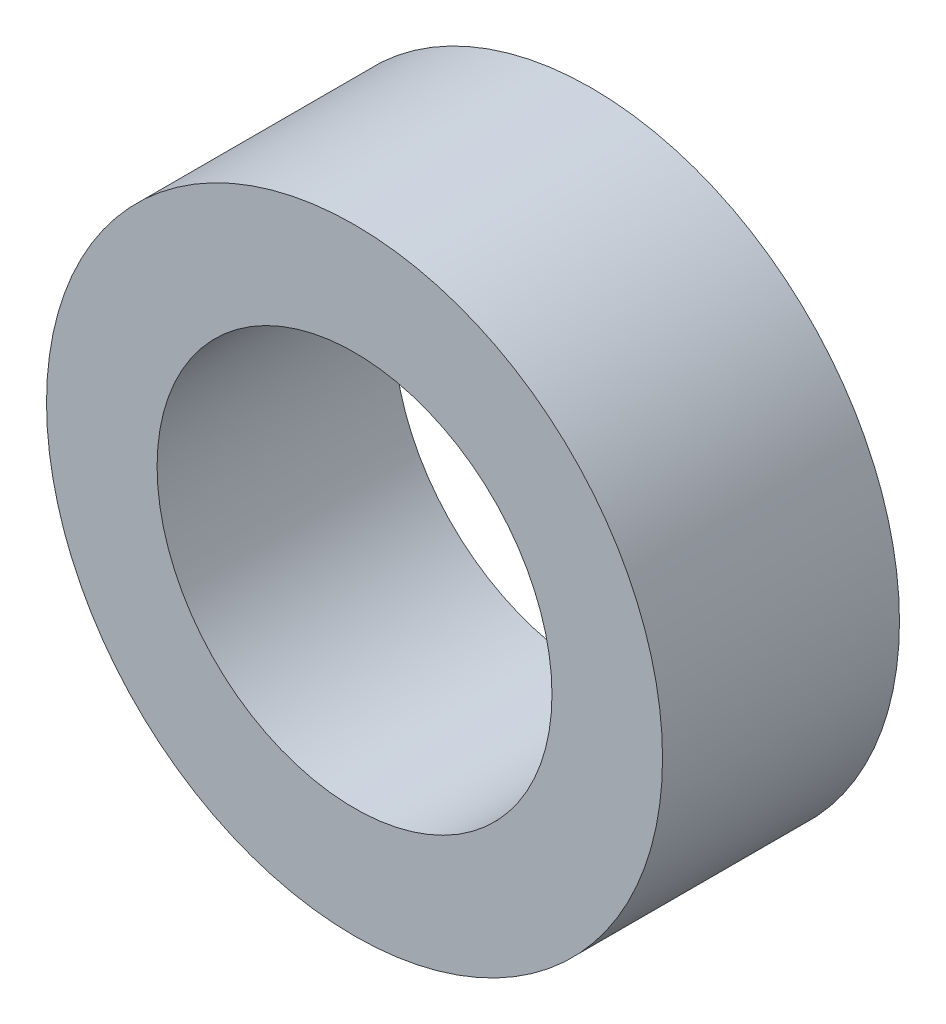
SolidWorks part; units mm, degrees
ref_plane "Plan de face" through (0, 0, 0) normal (0, 0, 1) x (1, 0, 0)
ref_plane "Plan de dessus" through (0, 0, 0) normal (0, 1, 0) x (1, 0, 0)
ref_plane "Plan de droite" through (0, 0, 0) normal (1, 0, 0) x (0, 0, -1)
sketch "Esquisse1" plane through (0, 0, 0) normal (0, 0, 1) x (1, 0, 0)
  circle A0 centre (0, 0) radius 7.8
  circle A1 centre (0, 0) radius 5
  dimension "D1" = 15.6
  dimension "D2" = 10
extrude "Boss.-Extru.1" add sketch "Esquisse1" along normal blind 6
